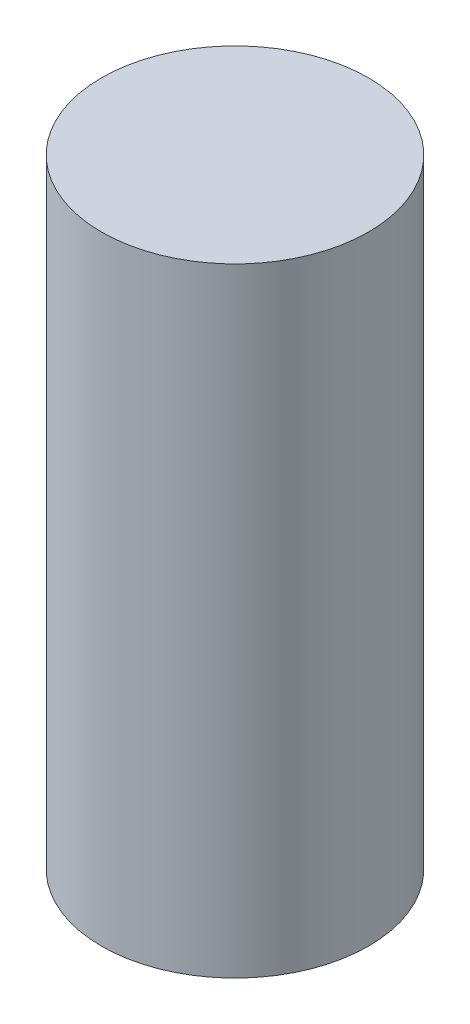
SolidWorks part; units mm, degrees
ref_plane "Front Plane" through (0, 0, 0) normal (0, 0, 1) x (1, 0, 0)
ref_plane "Top Plane" through (0, 0, 0) normal (0, 1, 0) x (1, 0, 0)
ref_plane "Right Plane" through (0, 0, 0) normal (1, 0, 0) x (0, 0, -1)
sketch "Sketch1" plane through (0, 0, 0) normal (0, 1, 0) x (1, 0, 0)
  circle A0 centre (0, 0) radius 60.325
  dimension "D1" = 120.65
extrude "Boss-Extrude1" add sketch "Sketch1" along normal blind 279.4
